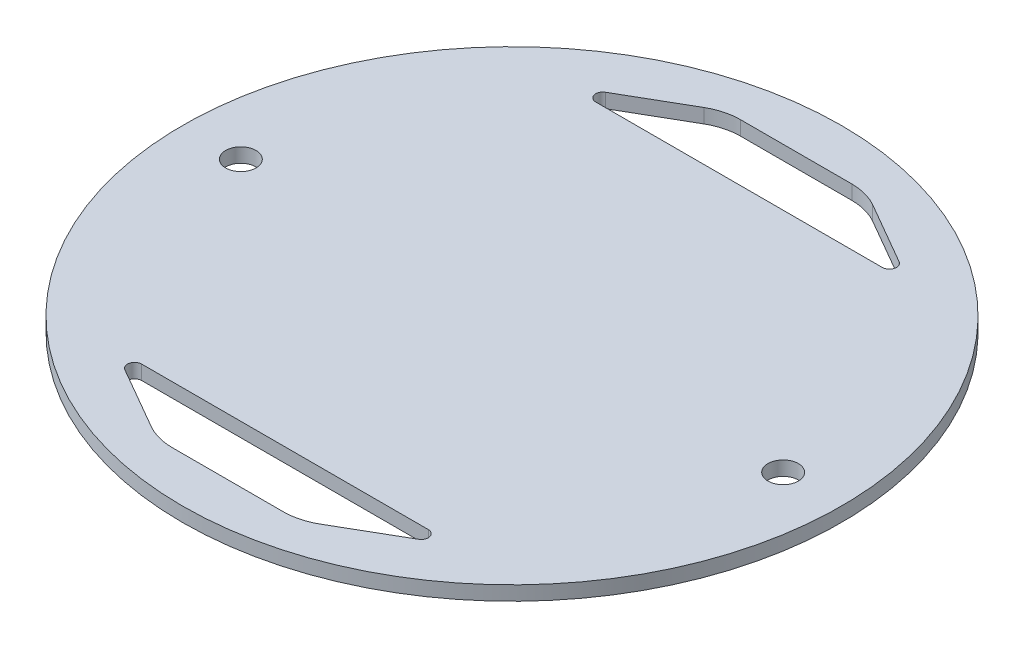
SolidWorks part; units mm, degrees
material "6061 Alloy"
ref_plane "Front Plane" through (0, 0, 0) normal (0, 0, 1) x (1, 0, 0)
ref_plane "Top Plane" through (0, 0, 0) normal (0, 1, 0) x (1, 0, 0)
ref_plane "Right Plane" through (0, 0, 0) normal (1, 0, 0) x (0, 0, -1)
sketch "Sketch2" plane through (0, 0, 0) normal (0, 1, 0) x (1, 0, 0)
  circle A0 centre (0, 0) radius 73.3171
  dimension "D1" = 146.6342
extrude "Boss-Extrude1" add sketch "Sketch2" along normal blind 3.175
sketch "Sketch3" plane through (0, 3.175, 0) normal (0, 1, 0) x (1, 0, 0)
  point P0 (-60.325, 0)
  point P1 (60.325, 0)
  dimension "D1" = 60.325
  dimension "D2" = 60.325
hole_wizard "1/4 Clearance Hole1" positions "Sketch3" profile "Sketch4" hole size "1/4" standard "ANSI Inch" end condition through all
sketch "Sketch4" plane through (-60.325, 3.175, 0) normal (1, 0, 0) x (0, 0, 1)
  line L0 (0, 0) -> (0, 3.175)
  line L1 (0, 3.175) -> (3.3782, 3.175)
  line L2 (3.3782, 3.175) -> (3.3782, 0)
  line L5 (3.3782, 0) -> (0, 0)
  line L11 (0, -6.35) -> (0, 107.95) construction
  dimension "Thru Hole Dia." = 6.7564
  dimension "Thru Hole Depth" = 3.175
sketch "Sketch5" plane through (0, 3.175, 0) normal (0, 1, 0) x (1, 0, 0)
  line L0 (-15.803, 63.2) -> (15.803, 63.2)
  line L1 (-50.5, -50.5) -> (50.5, -50.5) construction
  line L2 (-50.5, -50.5) -> (-50.5, 50.5) construction
  line L3 (-50.5, 50.5) -> (50.5, 50.5) construction
  line L4 (50.5, -50.5) -> (50.5, 50.5) construction
  line L5 (-50.5, -50.5) -> (50.5, 50.5) construction
  line L6 (-50.5, 50.5) -> (50.5, -50.5) construction
  line L7 (15.803, 63.2) -> (37.8, 50.5)
  line L8 (-15.803, 63.2) -> (-37.8, 50.5)
  line L9 (-50.5, 0) -> (50.5, 0) construction
  line L10 (0, 63.2) -> (0, 50.5)
  line L11 (-37.8, 50.5) -> (37.8, 50.5)
  point P0 (0, 0)
  dimension "D1" = 101
  dimension "D2" = 101
  dimension "D3" = 12.7
  dimension "D4" = 30
  dimension "D5" = 12.7
  dimension "D6" = 12.7
extrude "Cut-Extrude1" cut sketch "Sketch5" against normal through all both and the other way through all contours L8 L11 L10 L0 | L10 L11 L7 L0
fillet "Fillet1" radius 12.7 2 edges at (15.803, 1.5875, -63.2) (-15.803, 1.5875, -63.2)
fillet "Fillet2" radius 1.5875 2 edges at (37.8, 1.5875, -50.5) (-37.8, 1.5875, -50.5)
mirror "Mirror1" about plane through (0, 0, 0) normal (0, 0, 1) of "Cut-Extrude1", "Fillet1", "Fillet2"
equation "\"outerdiameter\"= 5.773"
equation "\"D1@Sketch2\"=\"outerdiameter\""
equation "\"platethickness\"= 1 / 8"
equation "\"holespacing\"= 2.375"
equation "\"D1@Sketch3\"=\"holespacing\""
equation "\"D2@Sketch3\"=\"holespacing\""
equation "\"D1@Boss-Extrude1\"=\"platethickness\""
